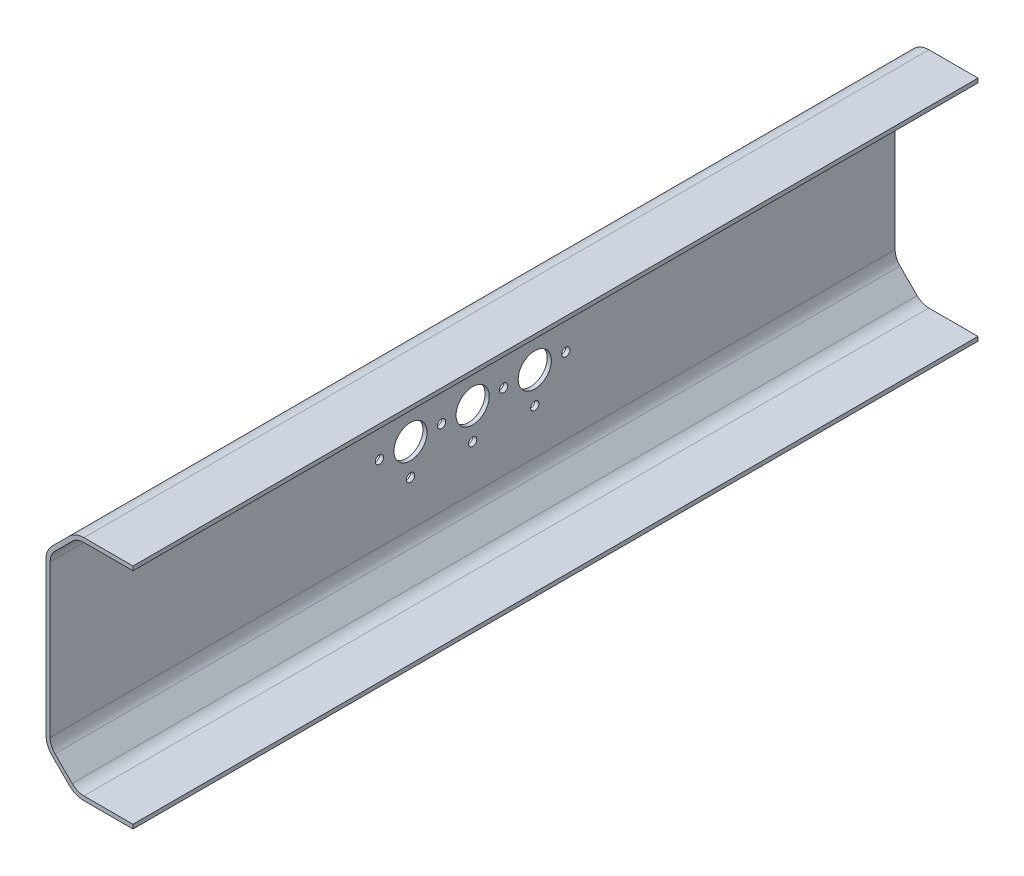
SolidWorks part; units mm, degrees
material "Alliage 1060"
ref_plane "Plan de face" through (0, 0, 0) normal (0, 0, 1) x (1, 0, 0)
ref_plane "Plan de dessus" through (0, 0, 0) normal (0, 1, 0) x (1, 0, 0)
ref_plane "Plan de droite" through (0, 0, 0) normal (1, 0, 0) x (0, 0, -1)
sketch "Esquisse1" plane through (0, 0, 0) normal (0, 0, 1) x (1, 0, 0)
  line L0 (-1.4645, 1.4645) -> (-5.6066, 5.6066)
  line L1 (-7.0711, 9.1421) -> (-7.0711, 45.8579)
  line L2 (-5.6066, 49.3934) -> (-1.4645, 53.5355)
  line L3 (2.0711, 55) -> (13.9289, 55)
  line L11 (13.9289, 0) -> (2.0711, 0)
  line L12 (13.9289, 1) -> (2.0711, 1)
  line L13 (-0.7574, 2.1716) -> (-4.8995, 6.3137)
  line L14 (-6.0711, 9.1421) -> (-6.0711, 45.8579)
  line L15 (-4.8995, 48.6863) -> (-0.7574, 52.8284)
  line L16 (2.0711, 54) -> (13.9289, 54)
  line L17 (13.9289, 0) -> (13.9289, 1)
  line L18 (13.9289, 55) -> (13.9289, 54)
  arc A0 (-1.4645, 1.4645) -> (2.0711, 0) centre (2.0711, 5) ccw
  arc A1 (-5.6066, 5.6066) -> (-7.0711, 9.1421) centre (-2.0711, 9.1421) cw
  arc A2 (-7.0711, 45.8579) -> (-5.6066, 49.3934) centre (-2.0711, 45.8579) cw
  arc A3 (-1.4645, 53.5355) -> (2.0711, 55) centre (2.0711, 50) cw
  arc A4 (-0.7574, 2.1716) -> (2.0711, 1) centre (2.0711, 5) ccw
  arc A5 (-4.8995, 6.3137) -> (-6.0711, 9.1421) centre (-2.0711, 9.1421) cw
  arc A6 (-6.0711, 45.8579) -> (-4.8995, 48.6863) centre (-2.0711, 45.8579) cw
  arc A7 (-0.7574, 52.8284) -> (2.0711, 54) centre (2.0711, 50) cw
  point P11 (0, 0)
  point P16 (-7.0711, 7.0711)
  point P19 (-7.0711, 47.9289)
  point P22 (0, 55)
  dimension "D6" = 5
  dimension "D1" = 21
  dimension "D2" = 45
  dimension "D3" = 45
  dimension "D4" = 53
  dimension "D5" = 10
  dimension "D7" = 1
extrude "Boss.-Extru.1" add sketch "Esquisse1" along normal blind 204
sketch "Esquisse2" plane through (-7.0711, 0, 0) normal (-1, 0, 0) x (0, 0, 1)
  line L0 (102, 55) -> (102, 0) construction
  line L1 (204, 55) -> (0, 55) construction
  line L2 (204, 0) -> (0, 0) construction
  circle A0 centre (102, 27.5) radius 4
  circle A1 centre (102, 35) radius 1
  circle A3 centre (109.5, 27.5) radius 1
  circle A4 centre (102, 20) radius 1
  circle A5 centre (94.5, 27.5) radius 1
  circle A6 centre (117, 27.5) radius 4
  circle A7 centre (117, 35) radius 1
  circle A8 centre (124.5, 27.5) radius 1
  circle A9 centre (117, 20) radius 1
  circle A11 centre (109.5, 27.5) radius 1 [skipped]
  circle A12 centre (87, 27.5) radius 4
  circle A13 centre (87, 35) radius 1
  circle A15 centre (87, 20) radius 1
  circle A16 centre (79.5, 27.5) radius 1
  circle A17 centre (94.5, 27.5) radius 1 [skipped]
  point P19 (102, 27.5)
  point P28 (117, 27.5)
  point P39 (87, 27.5)
  dimension "D1" = 8
  dimension "D2" = 2
  dimension "D4" = 15
  dimension "D6" = 15
  dimension "D8" = 15
  dimension "D5" = 2
  dimension "D7" = 2
  dimension "D3" = 4
extrude "Enlèv. mat.-Extru.1" cut sketch "Esquisse2" against normal through all
